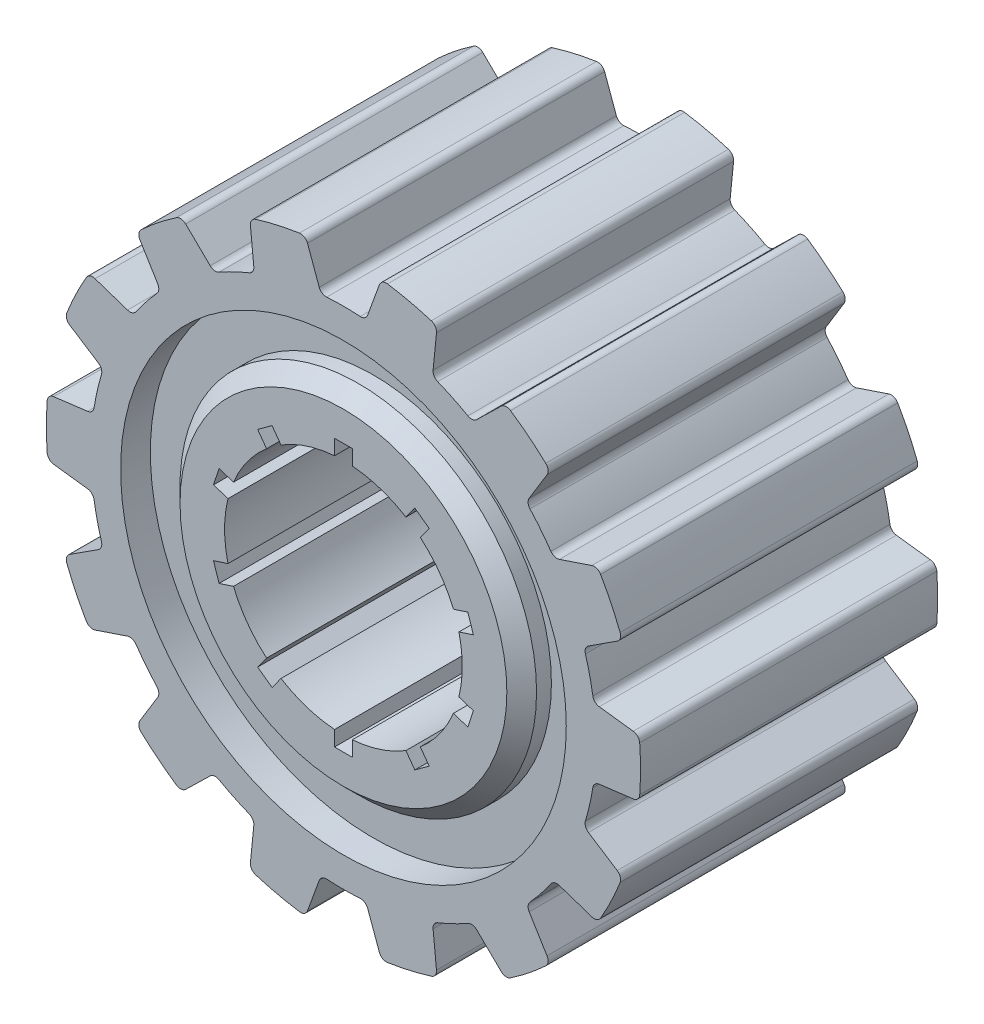
SolidWorks part; units mm, degrees
ref_plane "Front Plane" through (0, 0, 0) normal (0, 0, 1) x (1, 0, 0)
ref_plane "Top Plane" through (0, 0, 0) normal (0, 1, 0) x (1, 0, 0)
ref_plane "Right Plane" through (0, 0, 0) normal (1, 0, 0) x (0, 0, -1)
sketch "Sketch1" plane through (0, 0, 0) normal (0, 0, 1) x (1, 0, 0)
  line L0 (0, 0) -> (0, 21.3915) construction
  line L1 (2.4023, 3.8169) -> (2.1018, 3.4033)
  line L2 (-0.3, 4.5) -> (0.3, 4.5)
  line L3 (-0.3, 4.5) -> (-0.3, 3.9887)
  line L5 (0.3, 4.5) -> (0.3, 3.9887)
  line L6 (2.4023, 3.8169) -> (2.8877, 3.4642)
  line L7 (2.8877, 3.4642) -> (2.5872, 3.0506)
  line L8 (4.187, 1.6759) -> (3.7008, 1.5179)
  line L9 (4.187, 1.6759) -> (4.3725, 1.1053)
  line L10 (4.3725, 1.1053) -> (3.8862, 0.9473)
  line L11 (4.3725, -1.1053) -> (3.8862, -0.9473)
  line L12 (4.3725, -1.1053) -> (4.187, -1.6759)
  line L13 (4.187, -1.6759) -> (3.7008, -1.5179)
  line L14 (2.8877, -3.4642) -> (2.5872, -3.0506)
  line L15 (2.8877, -3.4642) -> (2.4023, -3.8169)
  line L16 (2.4023, -3.8169) -> (2.1018, -3.4033)
  line L17 (0.3, -4.5) -> (0.3, -3.9887)
  line L18 (0.3, -4.5) -> (-0.3, -4.5)
  line L19 (-0.3, -4.5) -> (-0.3, -3.9887)
  line L20 (-2.4023, -3.8169) -> (-2.1018, -3.4033)
  line L21 (-2.4023, -3.8169) -> (-2.8877, -3.4642)
  line L22 (-2.8877, -3.4642) -> (-2.5872, -3.0506)
  line L23 (-4.187, -1.6759) -> (-3.7008, -1.5179)
  line L24 (-4.187, -1.6759) -> (-4.3725, -1.1053)
  line L25 (-4.3725, -1.1053) -> (-3.8862, -0.9473)
  line L26 (-4.3725, 1.1053) -> (-3.8862, 0.9473)
  line L27 (-4.3725, 1.1053) -> (-4.187, 1.6759)
  line L28 (-4.187, 1.6759) -> (-3.7008, 1.5179)
  line L29 (-2.8877, 3.4642) -> (-2.5872, 3.0506)
  line L30 (-2.8877, 3.4642) -> (-2.4023, 3.8169)
  line L31 (-2.4023, 3.8169) -> (-2.1018, 3.4033)
  circle A0 centre (0, 0) radius 10
  arc A1 (-0.3, 3.9887) -> (-2.1018, 3.4033) centre (0, 0) ccw
  arc A2 (-2.5872, 3.0506) -> (-3.7008, 1.5179) centre (0, 0) ccw
  arc A3 (2.1018, 3.4033) -> (0.3, 3.9887) centre (0, 0) ccw
  arc A4 (3.7008, 1.5179) -> (2.5872, 3.0506) centre (0, 0) ccw
  arc A5 (0.3, -3.9887) -> (2.1018, -3.4033) centre (0, 0) ccw
  arc A6 (2.5872, -3.0506) -> (3.7008, -1.5179) centre (0, 0) ccw
  arc A7 (3.8862, -0.9473) -> (3.8862, 0.9473) centre (0, 0) ccw
  arc A8 (-2.1018, -3.4033) -> (-0.3, -3.9887) centre (0, 0) ccw
  arc A9 (-3.7008, -1.5179) -> (-2.5872, -3.0506) centre (0, 0) ccw
  arc A10 (-3.8862, 0.9473) -> (-3.8862, -0.9473) centre (0, 0) ccw
  point P47 (0, 0)
  dimension "D1" = 20
  dimension "D2" = 8
  dimension "D3" = 0.6
  dimension "D4" = 4.5
  dimension "D5" = 10
extrude "Boss-Extrude1" add sketch "Sketch1" along normal blind 10
sketch "Sketch2" plane through (0, 0, 10) normal (0, 0, 1) x (1, 0, 0)
  line L0 (0, 0) -> (0, 14.9505) construction
  line L2 (0.75, 8.4668) -> (1.2782, 9.918)
  line L3 (-0.75, 8.4668) -> (-1.2782, 9.918)
  circle A0 centre (0, 0) radius 10 construction
  arc A1 (1.2782, 9.918) -> (-1.2782, 9.918) centre (0, 0) ccw
  arc A2 (-0.75, 8.4668) -> (0.75, 8.4668) centre (0, 0) cw
  point P8 (0, 8.5)
  dimension "D1" = 1.5
  dimension "D2" = 20
  dimension "D3" = 20
  dimension "D4" = 8.5
extrude "Cut-Extrude1" cut sketch "Sketch2" against normal through all contours A1 L3 A2 L2
pattern_circular "CirPattern1" count 14 over 360 about axis through (0, 0, 0) along (0, 0, 1) of "Cut-Extrude1"
ref_plane "Plane1" through (0, 0, 5) normal (0, 0, 1) x (1, 0, 0)
sketch "Sketch3" plane through (0, 0, 5) normal (0, 0, 1) x (1, 0, 0)
  circle A0 centre (0, 0) radius 7.5
  circle A1 centre (0, 0) radius 6
  dimension "D1" = 15
  dimension "D2" = 12
extrude "Cut-Extrude2" cut sketch "Sketch3" against normal through all from offset 4 offset against normal yes
chamfer "Chamfer1" distance 0.5 angle 45 1 edges at (6, 0, 0)
mirror "Mirror2" about plane through (0, 0, 5) normal (0, 0, 1) of "Cut-Extrude2"
chamfer "Chamfer2" distance 0.5 angle 45 1 edges at (6, 0, 10)
fillet "Fillet1" radius 0.25 56 edges at (-7.0873, 4.6926, 5) (-8.5511, 5.1844, 5) (-9.3849, 3.4531, 5) (-8.0877, 2.6152, 5) (-8.4215, 1.1529, 5) (-9.9537, 0.9608, 5) (-9.9537, -0.9608, 5) (-8.4215, -1.1529, 5) (-8.0877, -2.6152, 5) (-9.3849, -3.4531, 5) (-8.5511, -5.1844, 5) (-7.0873, -4.6926, 5) (-6.152, -5.8654, 5) (-6.9573, -7.1831, 5) (-5.4548, -8.3812, 5) (-4.3494, -7.303, 5) (-2.9979, -7.9538, 5) (-3.1517, -9.4904, 5) (-1.2782, -9.918, 5) (-0.75, -8.4668, 5) (0.75, -8.4668, 5) (1.2782, -9.918, 5) (3.1517, -9.4904, 5) (2.9979, -7.9538, 5) (4.3494, -7.303, 5) (5.4548, -8.3812, 5) (6.9573, -7.1831, 5) (6.152, -5.8654, 5) (7.0873, -4.6926, 5) (8.5511, -5.1844, 5) (9.3849, -3.4531, 5) (8.0877, -2.6152, 5) (8.4215, -1.1529, 5) (9.9537, -0.9608, 5) (9.9537, 0.9608, 5) (8.4215, 1.1529, 5) (8.0877, 2.6152, 5) (9.3849, 3.4531, 5) (8.5511, 5.1844, 5) (7.0873, 4.6926, 5) (6.152, 5.8654, 5) (6.9573, 7.1831, 5) (5.4548, 8.3812, 5) (4.3494, 7.303, 5) (2.9979, 7.9538, 5) (3.1517, 9.4904, 5) (1.2782, 9.918, 5) (0.75, 8.4668, 5) (-0.75, 8.4668, 5) (-3.1517, 9.4904, 5) (-2.9979, 7.9538, 5) (-4.3494, 7.303, 5) (-5.4548, 8.3812, 5) (-6.9573, 7.1831, 5) (-6.152, 5.8654, 5) (-1.2782, 9.918, 5)
